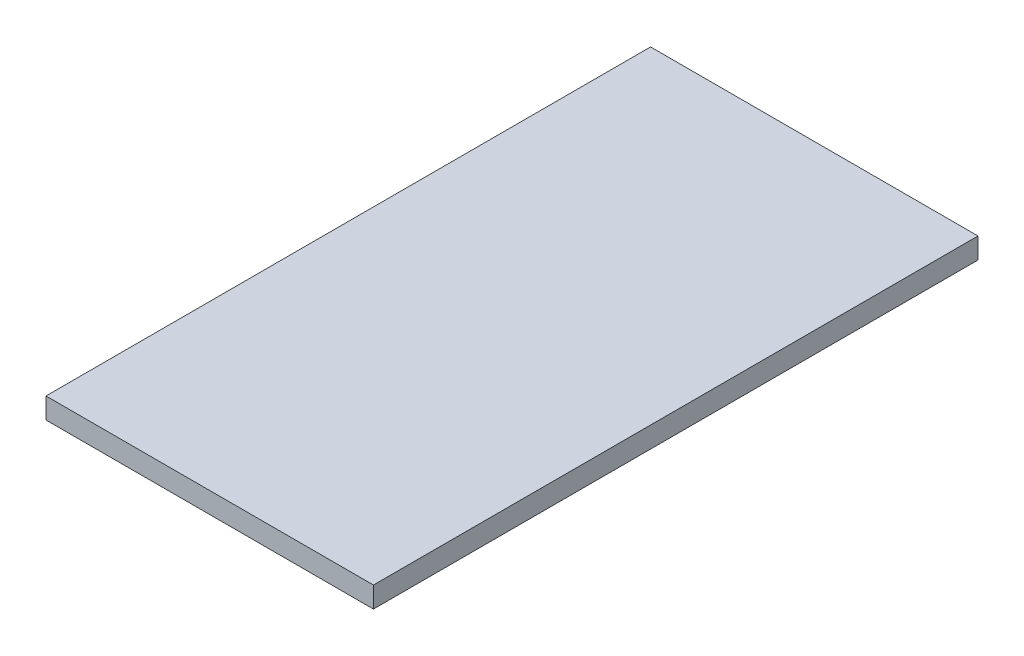
SolidWorks part; units mm, degrees
material "Oak"
ref_plane "Front Plane" through (0, 0, 0) normal (0, 0, 1) x (1, 0, 0)
ref_plane "Top Plane" through (0, 0, 0) normal (0, 1, 0) x (1, 0, 0)
ref_plane "Right Plane" through (0, 0, 0) normal (1, 0, 0) x (0, 0, -1)
sketch "Sketch1" plane through (0, 0, 0) normal (0, 1, 0) x (1, 0, 0)
  line L4 (299.212, 0) -> (299.212, 552.45)
  line L5 (299.212, 552.45) -> (0, 552.45)
  line L7 (0, 0) -> (299.212, 0)
  line L8 (0, 552.45) -> (0, 0)
  dimension "D1" = 299.212
  dimension "D5" = 552.45
extrude "Boss-Extrude1" add sketch "Sketch1" against normal blind 19.05
